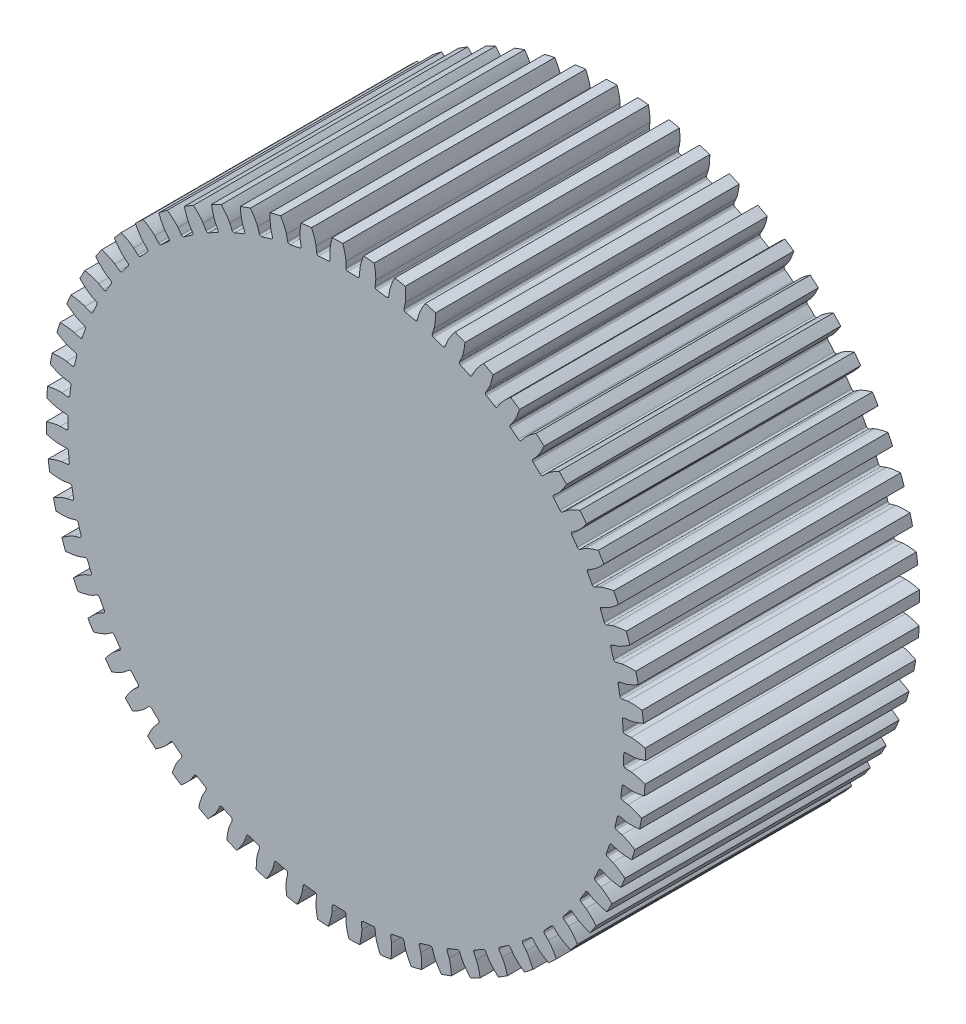
SolidWorks part; units mm, degrees
ref_plane "Front Plane" through (0, 0, 0) normal (0, 0, 1) x (1, 0, 0)
ref_plane "Top Plane" through (0, 0, 0) normal (0, 1, 0) x (1, 0, 0)
ref_plane "Right Plane" through (0, 0, 0) normal (1, 0, 0) x (0, 0, -1)
sketch "Sketch1" plane through (0, 0, 0) normal (0, 0, 1) x (1, 0, 0)
  circle A0 centre (0, 0) radius 24.0452
  dimension "D1" = 48.0904
extrude "Boss-Extrude1" add sketch "Sketch1" along normal blind 22.0082 contours A0
sketch "Sketch2" plane through (0, 0, 0) normal (0, 0, 1) x (1, 0, 0)
  line L0 (0, 0) -> (22.916, 0) construction
  line L1 (0, 0) -> (24.0381, -0.5863) construction
  line L2 (0, 0) -> (22.8888, -1.1172) construction
  line L3 (22.3, 0) -> (22.916, 0)
  line L4 (22.2735, -1.0872) -> (22.8888, -1.1172)
  circle A0 centre (0, 0) radius 23.2696 construction
  circle A1 centre (0, 0) radius 22.916 construction
  arc A2 (22.2735, -1.0872) -> (22.3, 0) centre (0, 0) ccw
  circle A3 centre (0, 0) radius 24.0452 construction
  spline S0 degree 4 poles (22.916, 0) (22.933, 0.0004) (22.9805, 0.0025) (23.07, 0.0109) (23.2156, 0.0307) (23.3999, 0.0651) (23.6364, 0.1199) (23.9123, 0.1977) (24.2123, 0.2969) (24.5345, 0.4194) (24.8519, 0.5545) (25.1643, 0.7009) (25.4716, 0.8575) (25.8386, 1.059) (26.2717, 1.3183) (26.7654, 1.644) (27.312, 2.0436) (27.8501, 2.4766) (28.3681, 2.931) (28.8687, 3.4082) (29.3482, 3.9007) (29.8132, 4.4167) (30.1976, 4.8722) (30.5259, 5.2876) (30.7761, 5.6149) (30.9987, 5.9221) (31.2122, 6.2177) (31.5527, 6.7251) (31.759, 7.0448) (32.0694, 7.5493) (32.1762, 7.7374) (32.2638, 7.8867) knots 0 0 0 0 0 0.005377 0.015084 0.028532 0.04661 0.064855 0.092111 0.119476 0.146842 0.174209 0.201575 0.228941 0.256307 0.307035 0.361767 0.4165 0.471232 0.525964 0.580697 0.635429 0.690161 0.744894 0.77226 0.799626 0.826992 0.854358 0.909091 0.954545 1 1 1 1 1 construction
  spline S1 degree 4 poles (22.916, 0) (22.933, 0.0004) (22.9805, 0.0025) (23.07, 0.0109) (23.2156, 0.0307) (23.3999, 0.0651) (23.6364, 0.1199) (23.9123, 0.1977) (24.2123, 0.2969) (24.5345, 0.4194) (24.8519, 0.5545) (25.1643, 0.7009) (25.4716, 0.8575) (25.8386, 1.059) (26.2717, 1.3183) (26.7654, 1.644) (27.312, 2.0436) (27.8501, 2.4766) (28.3681, 2.931) (28.8687, 3.4082) (29.3482, 3.9007) (29.8132, 4.4167) (30.1976, 4.8722) (30.5259, 5.2876) (30.7761, 5.6149) (30.9987, 5.9221) (31.2122, 6.2177) (31.4528, 6.5762) (31.5801, 6.7697) (31.6648, 6.9016) knots 0 0 0 0 0 0.005377 0.015084 0.028532 0.04661 0.064855 0.092111 0.119476 0.146842 0.174209 0.201575 0.228941 0.256307 0.307035 0.361767 0.4165 0.471232 0.525964 0.580697 0.635429 0.690161 0.744894 0.77226 0.799626 0.826992 0.854358 0.909091 0.909091 0.909091 0.909091 0.909091
  spline S2 degree 4 poles (22.8888, -1.1172) (22.9057, -1.1184) (22.953, -1.1228) (23.0421, -1.1356) (23.1865, -1.1625) (23.3689, -1.2058) (23.6025, -1.2721) (23.8743, -1.3632) (24.169, -1.4769) (24.4848, -1.615) (24.7953, -1.7654) (25.1002, -1.9269) (25.3996, -2.0983) (25.7563, -2.3174) (26.1762, -2.5975) (26.6534, -2.947) (27.1799, -3.3727) (27.6962, -3.8314) (28.1915, -4.3105) (28.6682, -4.8115) (29.1231, -5.3268) (29.5624, -5.8649) (29.9241, -6.3386) (30.2318, -6.7696) (30.4657, -7.1086) (30.6732, -7.4263) (30.872, -7.732) (31.1873, -8.2553) (31.3777, -8.5847) (31.6632, -9.1038) (31.7608, -9.2968) (31.8409, -9.4502) knots 0 0 0 0 0 0.005377 0.015084 0.028532 0.04661 0.064855 0.092111 0.119476 0.146842 0.174209 0.201575 0.228941 0.256307 0.307035 0.361767 0.4165 0.471232 0.525964 0.580697 0.635429 0.690161 0.744894 0.77226 0.799626 0.826992 0.854358 0.909091 0.954545 1 1 1 1 1 construction
  spline S3 degree 4 poles (22.8888, -1.1172) (22.9057, -1.1184) (22.953, -1.1228) (23.0421, -1.1356) (23.1865, -1.1625) (23.3689, -1.2058) (23.6025, -1.2721) (23.8743, -1.3632) (24.169, -1.4769) (24.4848, -1.615) (24.7953, -1.7654) (25.1002, -1.9269) (25.3996, -2.0983) (25.7563, -2.3174) (26.1762, -2.5975) (26.6534, -2.947) (27.1799, -3.3727) (27.6962, -3.8314) (28.1915, -4.3105) (28.6682, -4.8115) (29.1231, -5.3268) (29.5624, -5.8649) (29.9241, -6.3386) (30.2318, -6.7696) (30.4657, -7.1086) (30.6732, -7.4263) (30.872, -7.732) (31.0948, -8.1018) (31.2125, -8.3012) (31.2907, -8.4371) knots 0 0 0 0 0 0.005377 0.015084 0.028532 0.04661 0.064855 0.092111 0.119476 0.146842 0.174209 0.201575 0.228941 0.256307 0.307035 0.361767 0.4165 0.471232 0.525964 0.580697 0.635429 0.690161 0.744894 0.77226 0.799626 0.826992 0.854358 0.909091 0.909091 0.909091 0.909091 0.909091
  point P2 (0, 0)
  point P4 (0, 0)
  point P18 (24.1094, -3.0398)
  point P19 (24.0236, 0.0178)
  point P20 (0, 0)
  point P21 (0, 0)
  point P22 (0, 0)
  point P23 (0, 0)
  point P24 (0, 0)
  dimension "D1" = 46.5391
  dimension "D2" = 45.8321
  dimension "D3" = 44.6
  dimension "D4" = 1.397
  dimension "D5" = 1.397
extrude "Cut-Extrude3" cut sketch "Sketch2" against normal through all and the other way through all
fillet "Fillet1" radius 0.15 2 edges at (22.2735, -1.0872, 11.0041) (22.3, 0, 11.0041)
pattern_circular "CirPattern16" count 60 over 360 about axis through (0, 0, 22.0082) along (0, 0, -1) of "Fillet1", "Cut-Extrude3"
equation "\"P`\"= \"N\" / \"dp\"'Diametral pitch - number of teeth per mm"
equation "\"N\" = 60'# of teeth"
equation "\"phi\" = 10deg'Pressure angle"
equation "\"a\"= 1 / \"P`\"'Addendum"
equation "\"b\"= 1.25 / \"P`\"'Dedendum"
equation "\"c\"= \"b\" - \"a\"'clearance"
equation "\"dp\" = \"dp_from_dedendum\"'pitch cirle diameter"
equation "\"db\"= \"dp\" * cos ( \"phi\" )'base circle diameter"
equation "\"D1@Sketch1\" = \"dp\" + 2 * \"a\"'Addendum circle diameter"
equation "\"D1@Sketch2\"= \"dp\"'Pitch circle diameter"
equation "\"D2@Sketch2\"= \"db\" 'Base cicrle diameter"
equation "\"alpha\"= sqr ( \"dp\" ^ 2 - \"db\" ^ 2 ) / \"db\" * 180 / pi - \"phi\""
equation "\"dedendum_dia\" = 44.60mm"
equation "\"D3@Sketch2\"= \"dp\" - 2 * \"b\"'Dedendum circle diameter"
equation "\"D4@Sketch2\"= 360 / ( 4 * \"N\" ) - \"alpha\""
equation "\"D5@Sketch2\"= 360 / ( 4 * \"N\" ) - \"alpha\""
equation "\"dp_from_dedendum\"= \"dedendum_dia\" / ( 1 - ( 2.5 / \"N\" ) )"
